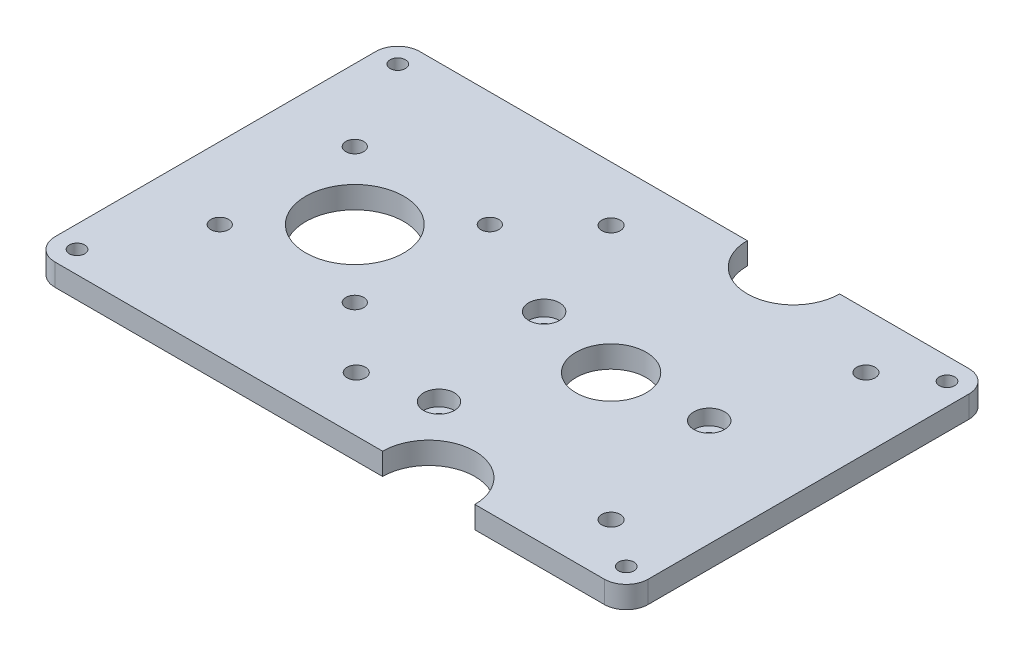
SolidWorks part; units mm, degrees
ref_plane "Front Plane" through (0, 0, 0) normal (0, 0, 1) x (1, 0, 0)
ref_plane "Top Plane" through (0, 0, 0) normal (0, 1, 0) x (1, 0, 0)
ref_plane "Right Plane" through (0, 0, 0) normal (1, 0, 0) x (0, 0, -1)
sketch "Sketch1" plane through (0, 0, 0) normal (0, 1, 0) x (1, 0, 0)
  line L0 (-67.5, 0) -> (67.5, 0) construction
  line L1 (67.5, -41.5) -> (33.05, -41.5)
  line L2 (67.5, -41.5) -> (67.5, 41.5)
  line L3 (67.5, 41.5) -> (33.05, 41.5)
  line L4 (-67.5, -41.5) -> (-67.5, 41.5)
  line L5 (67.5, -41.5) -> (-67.5, 41.5) construction
  line L6 (67.5, 41.5) -> (-67.5, -41.5) construction
  line L7 (22.55, 31.1) -> (22.55, -31.1) construction
  line L8 (49.455, -31.1) -> (-49.455, -31.1) construction
  line L9 (49.455, -31.1) -> (49.455, 31.1) construction
  line L10 (49.455, 31.1) -> (-49.455, 31.1) construction
  line L11 (-49.455, -31.1) -> (-49.455, 31.1) construction
  line L12 (49.455, -31.1) -> (-49.455, 31.1) construction
  line L13 (49.455, 31.1) -> (-49.455, -31.1) construction
  line L14 (0, 41.5) -> (0, -41.5) construction
  line L15 (12.05, -41.5) -> (-67.5, -41.5)
  line L16 (-51.147, -15.367) -> (-20.413, -15.367) construction
  line L17 (-51.147, -15.367) -> (-51.147, 15.367) construction
  line L18 (-51.147, 15.367) -> (-20.413, 15.367) construction
  line L19 (-20.413, -15.367) -> (-20.413, 15.367) construction
  line L20 (-51.147, -15.367) -> (-20.413, 15.367) construction
  line L21 (-51.147, 15.367) -> (-20.413, -15.367) construction
  line L22 (12.05, 41.5) -> (-67.5, 41.5)
  circle A0 centre (-6.45, 29) radius 2.1
  circle A1 centre (51.55, 29) radius 2.1
  circle A2 centre (51.55, -29) radius 2.1
  circle A3 centre (-6.45, -29) radius 2.1
  circle A4 centre (22.55, 0) radius 8
  circle A6 centre (-35.78, 0) radius 11.176
  circle A8 centre (-62.5, 36.5) radius 1.75
  circle A9 centre (62.5, 36.5) radius 1.75
  circle A10 centre (62.5, -36.5) radius 1.75
  circle A11 centre (-62.5, -36.5) radius 1.75
  circle A12 centre (-20.413, 15.367) radius 2.032
  circle A13 centre (-20.413, -15.367) radius 2.032
  circle A14 centre (-51.147, -15.367) radius 2.032
  circle A15 centre (-51.147, 15.367) radius 2.032
  arc A16 (33.05, -41.5) -> (12.05, -41.5) centre (22.55, -41.5) ccw
  arc A17 (12.05, 41.5) -> (33.05, 41.5) centre (22.55, 41.5) ccw
  point P0 (0, 0)
  point P13 (22.55, 0)
  point P18 (0, 0)
  point P27 (22.55, 0)
  dimension "D3" = 4.2
  dimension "D4" = 16
  dimension "D8" = 22.352
  dimension "D9" = 30.734
  dimension "D17" = 3.5
  dimension "D19" = 5
  dimension "D12" = 4.064
  dimension "D20" = 4.064
  dimension "D21" = 4.064
  dimension "D22" = 4.064
  dimension "D23" = 21
  dimension "D24" = 21
  dimension "D25" = 5
  dimension "D26" = 5
  dimension "D1" = 135
  dimension "D2" = 83
  dimension "D5" = 29
  dimension "D6" = 29
  dimension "D7" = 29
  dimension "D10" = 58.33
  dimension "D11" = 30.734
  dimension "D13" = 98.91
  dimension "D14" = 62.2
  dimension "D15" = 72.005
  dimension "D16" = 98.91
  dimension "D18" = 5
extrude "Boss-Extrude1" add sketch "Sketch1" along normal blind 5
sketch "Sketch3" plane through (0, 5, 0) normal (0, 1, 0) x (1, 0, 0)
  line L1 (-29.93, -5.85) -> (-52.93, -5.85)
  line L2 (-29.93, -5.85) -> (-29.93, 5.85)
  line L3 (-29.93, 5.85) -> (-52.93, 5.85)
  line L4 (-52.93, -5.85) -> (-52.93, 5.85)
  line L5 (-29.93, 0) -> (-41.63, 0) construction
  circle A2 centre (-35.78, 0) radius 5.85 construction
  circle A3 centre (-35.78, 0) radius 11.176 construction
  circle A4 centre (-27.43, 0) radius 1
  circle A5 centre (-56.43, 0) radius 1
  dimension "D3" = 11.7
  dimension "D2" = 2
  dimension "D5" = 2
  dimension "D1" = 23
  dimension "D4" = 2.5
  dimension "D6" = 3.5
extrude "Cut-Extrude1" [suppressed] cut sketch "Sketch3" against normal through all
sketch "Sketch4" [suppressed] plane through (0, 5, 0) normal (0, 1, 0) x (1, 0, 0)
  line L0 (-45.3026, 5.85) -> (-52.93, 5.85) construction
  line L1 (-52.93, -5.85) -> (-45.3026, -5.85) construction
  line L2 (-29.93, -5.85) -> (-29.93, 5.85) construction
  circle A0 centre (-35.78, 0) radius 5.85
sketch "Sketch5" plane through (0, 5, 0) normal (0, 1, 0) x (1, 0, 0)
  line L1 (-10.0733, -32.5804) -> (55.1733, -32.5804)
  line L2 (-10.0733, -32.5804) -> (-10.0733, 32.5804)
  line L3 (-10.0733, 32.5804) -> (55.1733, 32.5804)
  line L4 (55.1733, -32.5804) -> (55.1733, 32.5804)
  line L5 (-10.0733, -32.5804) -> (55.1733, 32.5804) construction
  line L6 (-10.0733, 32.5804) -> (55.1733, -32.5804) construction
  circle A0 centre (22.55, 0) radius 31.4571
  point P0 (22.55, 0)
  circle M1 centre (-51.147, 15.367) radius 2.032
  circle M2 centre (-51.147, -15.367) radius 2.032
  circle M3 centre (-20.413, -15.367) radius 2.032
  circle M4 centre (-20.413, 15.367) radius 2.032
  circle M5 centre (62.5, 36.5) radius 1.75
  circle M6 centre (-62.5, 36.5) radius 1.75
  line M7 (67.5, -41.5) -> (67.5, 41.5)
  line M9 (67.5, 41.5) -> (33.05, 41.5)
  line M11 (-67.5, 41.5) -> (-67.5, -41.5)
  line M13 (33.05, -41.5) -> (67.5, -41.5)
  circle M19 centre (22.55, 0) radius 8
  circle M20 centre (-35.78, 0) radius 11.176
  circle M21 centre (62.5, -36.5) radius 1.75
  circle M22 centre (-62.5, -36.5) radius 1.75
  arc M30 (33.05, 41.5) -> (12.05, 41.5) centre (22.55, 41.5) cw
  line M31 (12.05, 41.5) -> (-67.5, 41.5)
  line M32 (-67.5, -41.5) -> (12.05, -41.5)
  arc M33 (12.05, -41.5) -> (33.05, -41.5) centre (22.55, -41.5) cw
extrude "Cut-Extrude2" [suppressed] cut sketch "Sketch5" against normal blind 10 contours L2 L3 L1 M30 M31 M11 M32 M33 M2 M4 M6 M20 M22 M3 M1 | A0 M33 M30 M19 | L4 L1 L3 M33 M13 M7 M9 M30 M5 M21
fillet "Fillet1" radius 5 4 edges at (-67.5, 2.5, 41.5) (-67.5, 2.5, -41.5) (67.5, 2.5, 41.5) (67.5, 2.5, -41.5)
sketch "Sketch8" plane through (0, 5, 0) normal (0, 1, 0) x (1, 0, 0)
  circle A7 centre (43.1993, 1.6821) radius 1.65
  circle A8 centre (2.9215, 4.384) radius 1.65
  circle A9 centre (8.6993, -25.3179) radius 1.65
  dimension "D1" = 3.3
  dimension "D2" = 3.3
  dimension "D3" = 3.3
extrude "Cut-Extrude3" cut sketch "Sketch8" against normal blind 10 contours A7 | A8 | A9
sketch "Sketch9" plane through (0, 5, 0) normal (0, 1, 0) x (1, 0, 0)
  circle A0 centre (43.1993, 1.6821) radius 3.5
  circle A1 centre (8.6993, -25.3179) radius 3.5
  circle A2 centre (2.9215, 4.384) radius 3.5
  circle M1 centre (43.1993, 1.6821) radius 1.65
  circle M2 centre (2.9215, 4.384) radius 1.65
  circle M3 centre (8.6993, -25.3179) radius 1.65
  dimension "D1" = 7
  dimension "D2" = 7
  dimension "D3" = 7
extrude "Cut-Extrude4" cut sketch "Sketch9" against normal blind 3.5 contours A2 M2 | A1 M3 | A0 M1
sketch "Sketch10" [suppressed] plane through (0, 5, 0) normal (0, 1, 0) x (1, 0, 0)
  line L1 (28.0899, 32.5804) -> (15.0541, 32.5804)
  line L2 (28.0899, 32.5804) -> (28.0899, 31.1354)
  line L3 (28.0899, 31.1354) -> (15.0541, 31.1354)
  line L4 (15.0541, 32.5804) -> (15.0541, 31.1354)
  line L5 (28.0899, -32.5804) -> (15.0541, -32.5804)
  line L6 (28.0899, -32.5804) -> (28.0899, -31.3439)
  line L7 (28.0899, -31.3439) -> (15.0541, -31.3439)
  line L8 (15.0541, -32.5804) -> (15.0541, -31.3439)
extrude "Boss-Extrude2" [suppressed] add sketch "Sketch10" against normal through all
sketch "Sketch11" plane through (0, 5, 0) normal (0, 1, 0) x (1, 0, 0)
  line L6 (-67.5, 36.5) -> (-67.5, -36.5)
  line L7 (-62.5, -41.5) -> (12.05, -41.5)
  line L8 (33.05, -41.5) -> (62.5, -41.5)
  line L9 (67.5, -36.5) -> (67.5, 36.5)
  line L10 (62.5, 41.5) -> (33.05, 41.5)
  line L11 (12.05, 41.5) -> (-62.5, 41.5)
  line L12 (-67.5, 36.5) -> (-67.5, -36.5)
  line L13 (-62.5, -41.5) -> (12.05, -41.5)
  line L14 (33.05, -41.5) -> (62.5, -41.5)
  line L15 (67.5, -36.5) -> (67.5, 36.5)
  line L16 (62.5, 41.5) -> (33.05, 41.5)
  line L17 (12.05, 41.5) -> (-62.5, 41.5)
  arc A6 (-67.5, -36.5) -> (-62.5, -41.5) centre (-62.5, -36.5) ccw
  arc A7 (33.05, -41.5) -> (12.05, -41.5) centre (22.55, -41.5) ccw
  arc A8 (62.5, -41.5) -> (67.5, -36.5) centre (62.5, -36.5) ccw
  arc A9 (67.5, 36.5) -> (62.5, 41.5) centre (62.5, 36.5) ccw
  arc A10 (12.05, 41.5) -> (33.05, 41.5) centre (22.55, 41.5) ccw
  arc A11 (-62.5, 41.5) -> (-67.5, 36.5) centre (-62.5, 36.5) ccw
  arc A12 (-67.5, -36.5) -> (-62.5, -41.5) centre (-62.5, -36.5) ccw
  arc A13 (33.05, -41.5) -> (12.05, -41.5) centre (22.55, -41.5) ccw
  arc A14 (62.5, -41.5) -> (67.5, -36.5) centre (62.5, -36.5) ccw
  arc A15 (67.5, 36.5) -> (62.5, 41.5) centre (62.5, 36.5) ccw
  arc A16 (12.05, 41.5) -> (33.05, 41.5) centre (22.55, 41.5) ccw
  arc A17 (-62.5, 41.5) -> (-67.5, 36.5) centre (-62.5, 36.5) ccw
  dimension "D2" = 135
  dimension "D3" = 83
  dimension "D1" = 0
